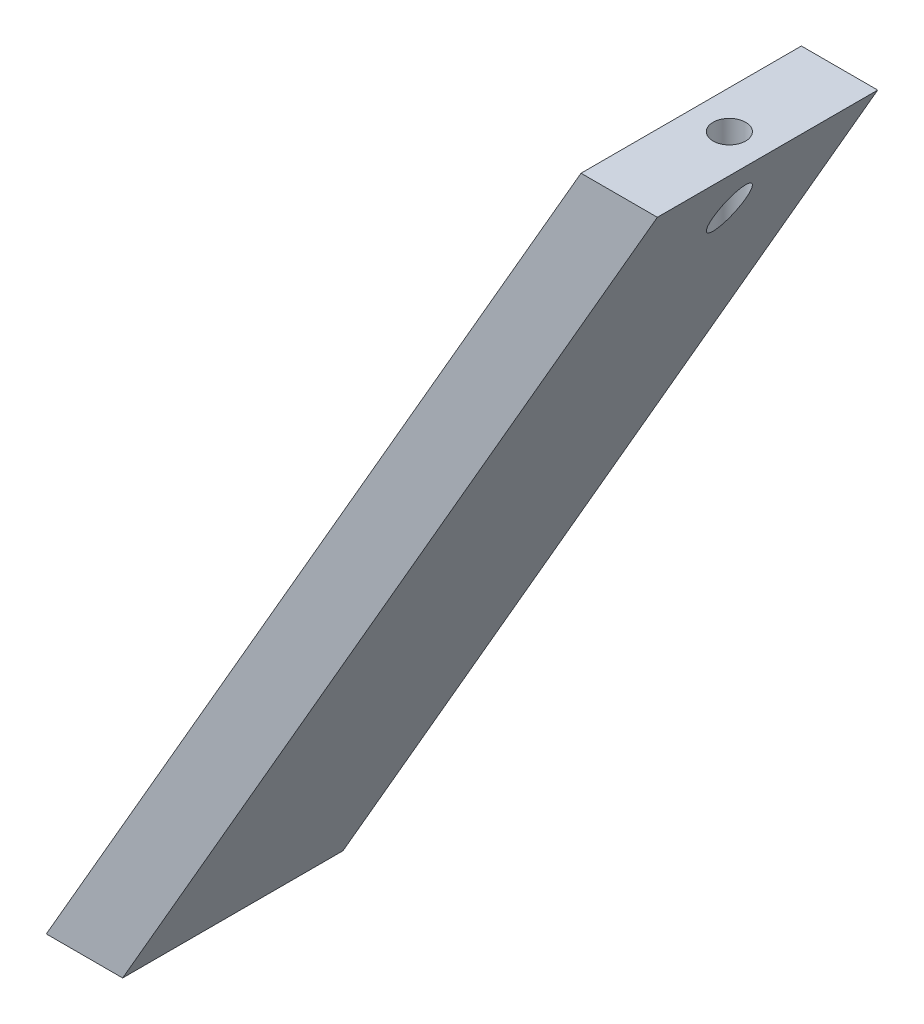
SolidWorks part; units mm, degrees
ref_plane "Front Plane" through (0, 0, 0) normal (0, 0, 1) x (1, 0, 0)
ref_plane "Top Plane" through (0, 0, 0) normal (0, 1, 0) x (1, 0, 0)
ref_plane "Right Plane" through (0, 0, 0) normal (1, 0, 0) x (0, 0, -1)
sketch "Left" plane through (0, 0, 0) normal (0, 0, 1) x (1, 0, 0)
  line L0 (-165.1, 19.05) -> (-10.9985, 285.9616)
  line L1 (-143.103, 19.05) -> (10.9985, 285.9616)
  line L3 (-165.1, 19.05) -> (-143.103, 19.05)
  line L5 (-10.9985, 285.9616) -> (10.9985, 285.9616)
  line L6 (-148.6022, 9.525) -> (16.4978, 295.4866) construction
  line L7 (-1143.103, 19.05) -> (48856.897, 19.05) construction
  line L8 (-165.1, 19.05) -> (0, 305.0116) construction
  point P1 (-63.5, 195.0264)
  point P9 (-148.6022, 9.525)
  point P10 (-47.0022, 185.5014)
  dimension "D1" = 60
  dimension "D2" = 19.05
extrude "left_ext" add sketch "Left" along normal blind 63.5
sketch "hole" plane through (0, 0, 0) normal (0, 1, 0) x (1, 0, 0)
  line L0 (0, -1000) -> (0, 49000) construction
  circle A0 centre (0, -31.75) radius 4.699
  dimension "D1" = 9.398
  dimension "D2" = 31.75
extrude "hole_cut" cut sketch "hole" along normal through all
